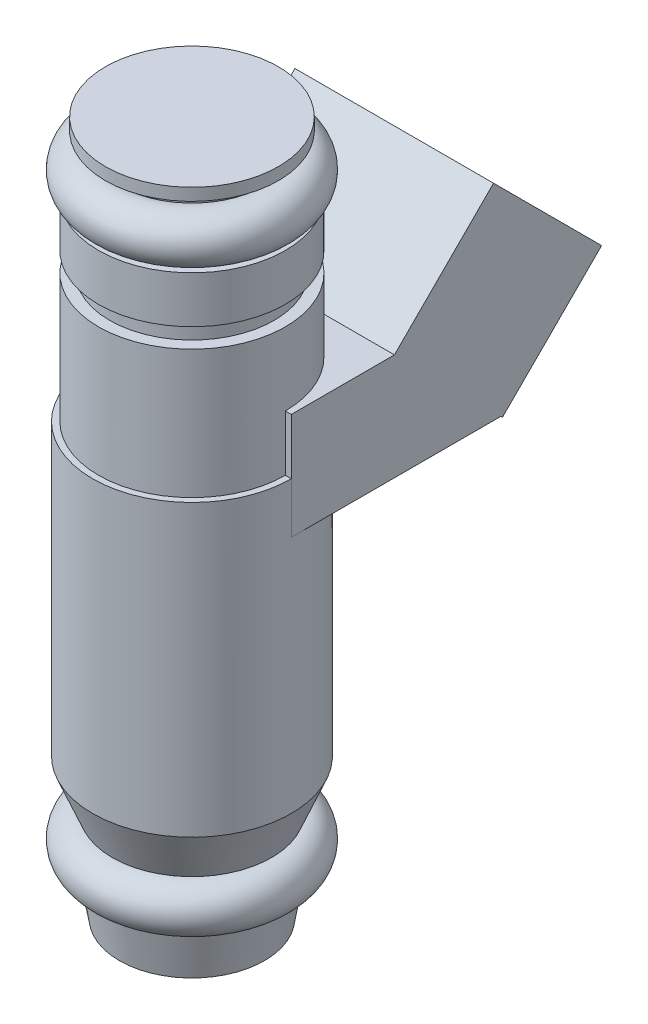
SolidWorks part; units mm, degrees
ref_plane "Front Plane" through (0, 0, 0) normal (0, 0, 1) x (1, 0, 0)
ref_plane "Top Plane" through (0, 0, 0) normal (0, 1, 0) x (1, 0, 0)
ref_plane "Right Plane" through (0, 0, 0) normal (1, 0, 0) x (0, 0, -1)
sketch "Sketch1" plane through (0, 0, 0) normal (1, 0, 0) x (0, 0, -1)
  line L0 (0, 42.4843) -> (0, -4.7157)
  line L1 (0, 42.4843) -> (-5.88, 42.4843)
  line L2 (-5.88, 42.4843) -> (-5.88, 41.6542)
  line L3 (-5.88, 41.6542) -> (-4.9336, 41.6542)
  line L4 (-4.9336, 41.6542) -> (-4.9336, 40.8836)
  line L5 (-5.4125, 37.7825) -> (-6.3463, 37.7825)
  line L6 (-6.3463, 34.6075) -> (-5.588, 34.6075)
  line L7 (-5.588, 34.6075) -> (-5.588, 33.2867)
  line L8 (-5.588, 33.2867) -> (-6.3463, 33.2867)
  line L9 (-6.3463, 33.2867) -> (-6.3463, 24.5525)
  line L10 (-6.3463, 24.5525) -> (-6.75, 24.5525)
  line L11 (-6.75, 24.5525) -> (-6.75, 4.8514)
  line L12 (-5.4125, 1.5875) -> (-6.75, 4.8514)
  line L13 (-5.5, -1.5851) -> (-4.9336, -4.7157)
  line L14 (-4.9336, -4.7157) -> (0, -4.7157)
  line L15 (-6.3463, 37.7825) -> (-6.3463, 34.6075)
  arc A0 (-4.9336, 40.8836) -> (-5.4125, 37.7825) centre (-5.4125, 39.37) ccw
  arc A1 (-5.4125, 1.5875) -> (-5.5, -1.5851) centre (-5.4125, 0) ccw
  dimension "D2" = 5.4125
  dimension "D3" = 3.175
  dimension "D1" = 39.37
  dimension "D4" = 5.588
  dimension "D5" = 1.3208
  dimension "D6" = 3.175
  dimension "D7" = 47.2
  dimension "D8" = 6.75
  dimension "D9" = 5.5
revolve "Revolve1" add sketch "Sketch1" angle 360 about L0
sketch "Sketch2" plane through (0, 0, 0) normal (1, 0, 0) x (0, 0, -1)
  line L0 (7.2319, 28.1141) -> (17.3319, 18.0141) construction
ref_plane "Plane1" through (0, 17.673, -17.673) normal (0, -0.7071, 0.7071) x (1, 0, 0)
sketch "Sketch3" plane through (0, 17.673, -17.673) normal (0, -0.7071, 0.7071) x (1, 0, 0)
  line L0 (6.75, 3.4305) -> (6.75, 17.3612) construction
  line L1 (6.75, 15.081) -> (-6.75, 15.081)
  line L2 (6.75, 15.081) -> (6.75, 4.6981)
  line L3 (6.75, 4.6981) -> (-6.75, 4.6981)
  line L4 (-6.75, 15.081) -> (-6.75, 4.6981)
  line L5 (-6.75, 17.3612) -> (-6.75, 3.4305) construction
extrude "Boss-Extrude1" add sketch "Sketch3" against normal blind 9.525 separate body
sketch "Sketch4" plane through (0, 0, 0) normal (0, 0, 1) x (1, 0, 0)
  line L0 (6.75, 4.8514) -> (6.75, 24.5525) construction
  line L1 (-6.75, 28.3369) -> (6.75, 28.3369)
  line L2 (-6.75, 28.3369) -> (-6.75, 21.1029)
  line L3 (-6.75, 21.1029) -> (6.75, 21.1029)
  line L4 (6.75, 28.3369) -> (6.75, 21.1029)
extrude "Boss-Extrude2" add sketch "Sketch4" against normal up to surface (7.0091 mm away)
